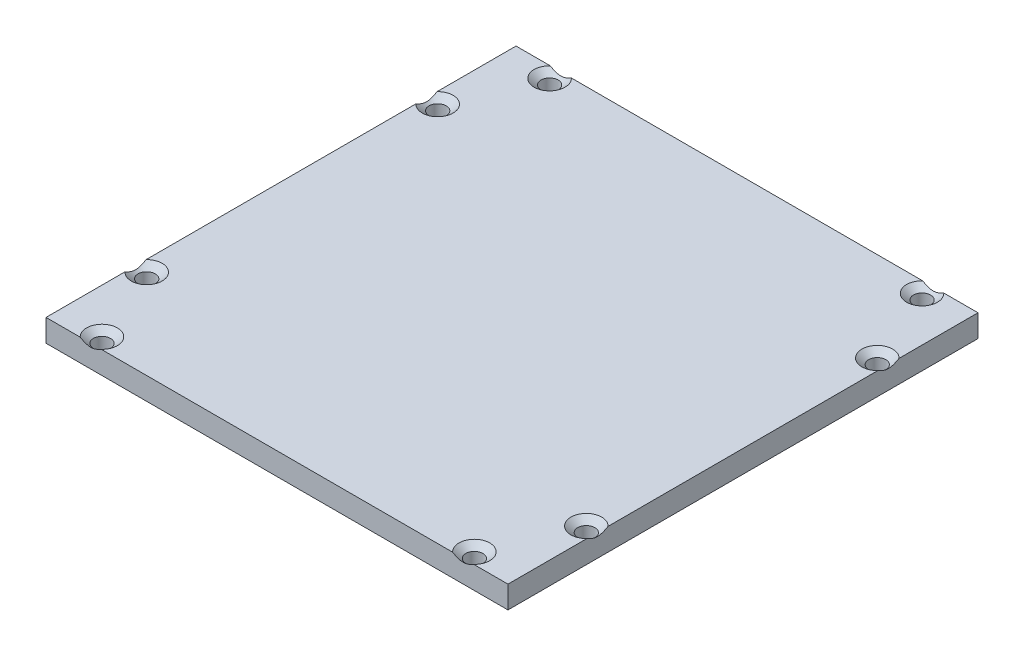
SolidWorks part; units mm, degrees
material "Delrin"
ref_plane "Front Plane" through (0, 0, 0) normal (0, 0, 1) x (1, 0, 0)
ref_plane "Top Plane" through (0, 0, 0) normal (0, 1, 0) x (1, 0, 0)
ref_plane "Right Plane" through (0, 0, 0) normal (1, 0, 0) x (0, 0, -1)
sketch "Sketch1" plane through (0, 0, 0) normal (0, 1, 0) x (1, 0, 0)
  line L1 (-32.766, 33.3375) -> (32.766, 33.3375)
  line L2 (-32.766, 33.3375) -> (-32.766, -33.3375)
  line L3 (-32.766, -33.3375) -> (32.766, -33.3375)
  line L4 (32.766, 33.3375) -> (32.766, -33.3375)
  dimension "D1" = 65.532
  dimension "D2" = 32.766
  dimension "D3" = 66.675
  dimension "D4" = 33.3375
extrude "Extrude1" add sketch "Sketch1" along normal blind 3.175
hole_wizard "CSK for #2 Flat Head Machine Screw (100)1" positions "3DSketch1" profile "Sketch2" countersink size "#2" standard "Ansi Inch" end condition through all
sketch3d "3DSketch1"
  line L0 (-32.766, 3.175, -33.3375) -> (-32.766, 3.175, 33.3375) construction
  line L1 (32.766, 3.175, 33.3375) -> (32.766, 3.175, -33.3375) construction
  line L2 (-32.766, 3.175, 33.3375) -> (32.766, 3.175, 33.3375) construction
  line L3 (32.766, 3.175, -33.3375) -> (-32.766, 3.175, -33.3375) construction
  point P1 (-26.416, 3.175, 31.75)
  point P3 (26.416, 3.175, 31.75)
  point P5 (26.416, 3.175, -31.75)
  point P7 (-26.416, 3.175, -31.75)
  point P9 (-31.1785, 3.175, -20.6375)
  point P11 (-31.1785, 3.175, 20.6375)
  point P13 (31.1785, 3.175, -20.6375)
  point P15 (31.1785, 3.175, 20.6375)
  dimension "D1" = 6.35
  dimension "D2" = 6.35
  dimension "D3" = 1.5875
  dimension "D4" = 1.5875
  dimension "D5" = 1.5875
  dimension "D6" = 1.5875
  dimension "D7" = 1.5875
  dimension "D8" = 1.5875
  dimension "D9" = 1.5875
  dimension "D10" = 1.5875
  dimension "D11" = 6.35
  dimension "D12" = 6.35
  dimension "D13" = 12.7
  dimension "D14" = 12.7
  dimension "D15" = 12.7
  dimension "D16" = 12.7
sketch "Sketch2" plane through (-26.416, 3.175, 31.75) normal (1, 0, 0) x (0, 0, 1)
  line L0 (0, 0) -> (0, 3.175)
  line L1 (0, 3.175) -> (1.2192, 3.175)
  line L2 (1.2192, 3.175) -> (1.2192, 0.8099)
  line L3 (1.2192, 0.8099) -> (2.1844, 0)
  line L5 (2.1844, 0) -> (0, 0)
  line L6 (-1.2192, 0.8099) -> (-2.1844, 0) construction
  line L11 (0, -6.35) -> (0, 107.95) construction
  dimension "Thru Hole Dia." = 2.4384
  dimension "Thru Hole Depth" = 3.175
  dimension "Near C'Sink Dia." = 4.3688
  dimension "Near C'Sink Angle" = 100
